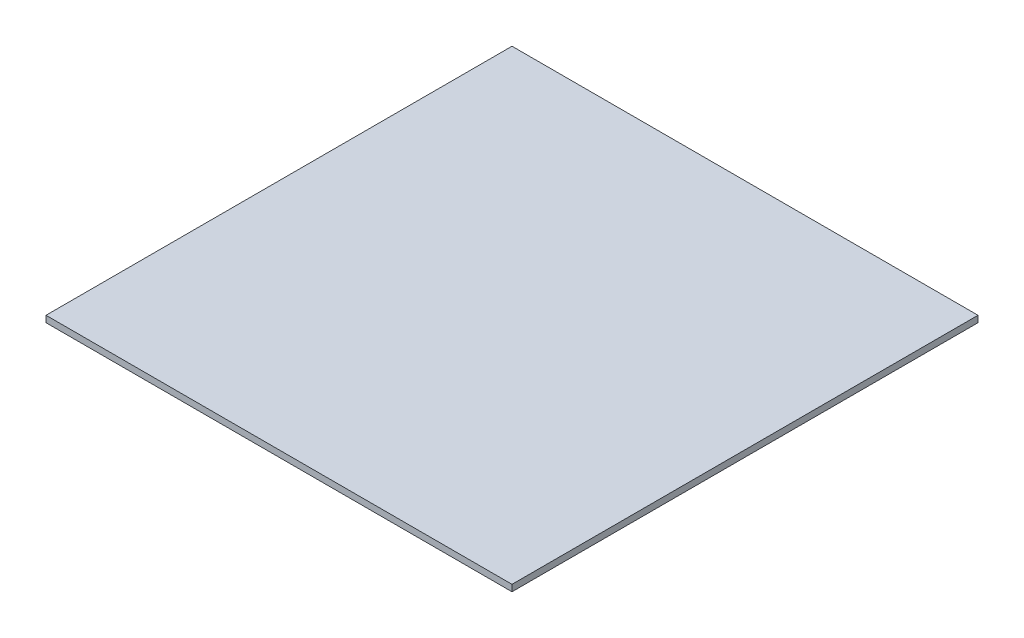
SolidWorks part; units mm, degrees
ref_plane "Front Plane" through (0, 0, 0) normal (0, 0, 1) x (1, 0, 0)
ref_plane "Top Plane" through (0, 0, 0) normal (0, 1, 0) x (1, 0, 0)
ref_plane "Right Plane" through (0, 0, 0) normal (1, 0, 0) x (0, 0, -1)
sketch "Sketch1" plane through (0, 0, 0) normal (0, 1, 0) x (1, 0, 0)
  line L1 (0, 0) -> (914.4, 0)
  line L2 (0, 0) -> (0, 914.4)
  line L3 (0, 914.4) -> (914.4, 914.4)
  line L4 (914.4, 0) -> (914.4, 914.4)
  dimension "D1" = 914.4
  dimension "D2" = 914.4
extrude "Boss-Extrude1" add sketch "Sketch1" along normal blind 12.7
